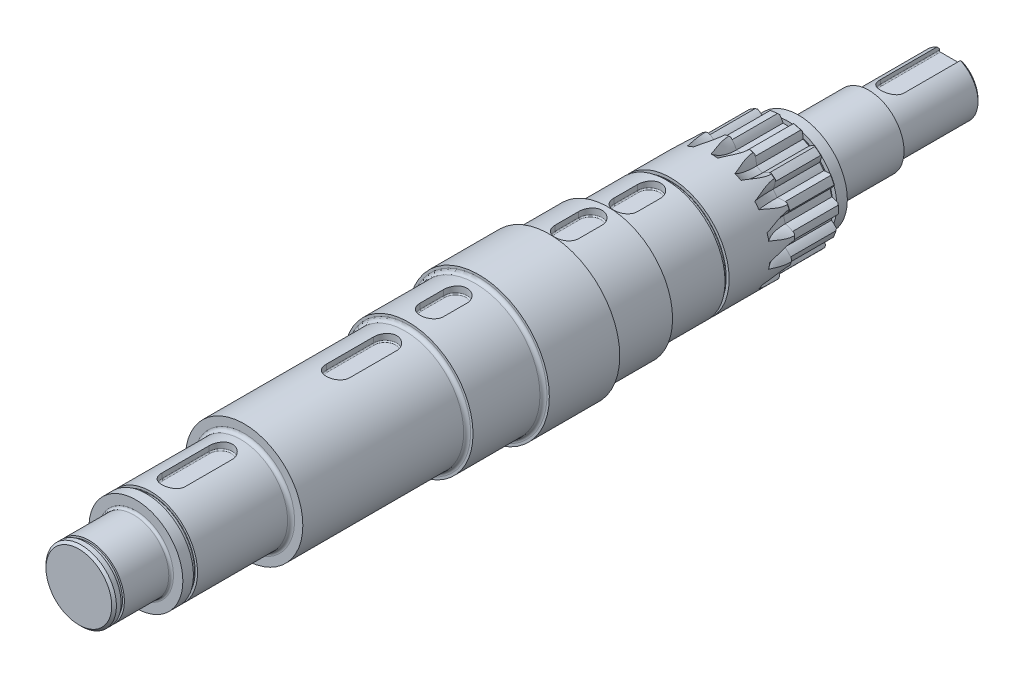
SolidWorks part; units mm, degrees
material "AISI 4340 Steel, annealed"
ref_plane "Front Plane" through (0, 0, 0) normal (0, 0, 1) x (1, 0, 0)
ref_plane "Top Plane" through (0, 0, 0) normal (0, 1, 0) x (1, 0, 0)
ref_plane "Right Plane" through (0, 0, 0) normal (1, 0, 0) x (0, 0, -1)
sketch "Sketch1" plane through (0, 0, 0) normal (1, 0, 0) x (0, 0, -1)
  line L0 (0, 0) -> (371.5, 0)
  line L2 (0, 15) -> (3, 15)
  line L3 (3, 15) -> (3, 14.175)
  line L4 (3, 14.175) -> (4.4, 14.175)
  line L5 (4.4, 14.175) -> (4.4, 15)
  line L6 (4.4, 15) -> (24.3, 15)
  line L7 (24.3, 15) -> (24.3, 20)
  line L12 (30.55, 20) -> (70.4, 20)
  line L13 (70.4, 20) -> (70.4, 25)
  line L14 (70.4, 25) -> (140.4, 25)
  line L15 (140.4, 25) -> (140.4, 27.5)
  line L16 (140.4, 27.5) -> (170.4, 27.5)
  line L20 (225.4, 25) -> (250.25, 25)
  line L21 (250.25, 25) -> (250.25, 23.6)
  line L22 (250.25, 23.6) -> (252, 23.6)
  line L23 (252, 23.6) -> (252, 25)
  line L24 (252, 25) -> (280.4, 25)
  line L25 (280.4, 25) -> (280.4, 23.85)
  line L26 (280.4, 23.85) -> (300.25, 23.85)
  line L27 (300.25, 23.85) -> (300.25, 18.85)
  line L28 (300.25, 18.85) -> (302, 18.85)
  line L29 (302, 18.85) -> (302, 20.85)
  line L30 (302, 20.85) -> (306.5, 20.85)
  line L31 (306.5, 20.85) -> (306.5, 15)
  line L32 (306.5, 15) -> (336.5, 15)
  line L34 (0, 15) -> (0, 0)
  line L35 (170.4, 27.5) -> (170.4, 30)
  line L36 (170.4, 30) -> (200.4, 30)
  line L37 (200.4, 30) -> (200.4, 27.5)
  line L38 (200.4, 27.5) -> (225.4, 27.5)
  line L39 (225.4, 27.5) -> (225.4, 25)
  line L40 (336.5, 15) -> (336.5, 12.5)
  line L41 (336.5, 12.5) -> (371.5, 12.5)
  line L42 (371.5, 12.5) -> (371.5, 0)
  line L43 (30.55, 20) -> (30.55, 18.85)
  line L44 (30.55, 18.85) -> (28.8, 18.85)
  line L45 (28.8, 18.85) -> (28.8, 20)
  line L46 (28.8, 20) -> (24.3, 20)
  point P1 (3.7, 14.175)
  dimension "D1" = 15
  dimension "D2" = 14.175
  dimension "D3" = 15
  dimension "D4" = 1.4
  dimension "D5" = 19.9
  dimension "D6" = 3
  dimension "D7" = 20
  dimension "D8" = 4.5
  dimension "D9" = 20
  dimension "D10" = 1.75
  dimension "D11" = 39.85
  dimension "D12" = 25
  dimension "D13" = 70
  dimension "D14" = 27.5
  dimension "D15" = 30
  dimension "D16" = 30
  dimension "D17" = 25
  dimension "D18" = 30
  dimension "D19" = 27.5
  dimension "D20" = 25
  dimension "D21" = 24.85
  dimension "D22" = 1.75
  dimension "D23" = 23.6
  dimension "D24" = 25
  dimension "D25" = 23.85
  dimension "D26" = 20.85
  dimension "D27" = 1.75
  dimension "D28" = 19.85
  dimension "D29" = 4.5
  dimension "D30" = 15
  dimension "D31" = 30
  dimension "D32" = 18.85
  dimension "D33" = 12.5
  dimension "D34" = 35
  dimension "D35" = 28.4
  dimension "D36" = 18.85
  dimension "D37" = 371.5
revolve "Revolve1" add sketch "Sketch1" angle 360 about L0
fillet "Fillet1" radius 1.5 5 edges at (25, 0, -225.4) (27.5, 0, -200.4) (20, 0, -70.4) (25, 0, -140.4) (27.5, 0, -170.4)
fillet "Fillet2" radius 1 3 edges at (15, 0, -306.5) (15, 0, -24.3) (12.5, 0, -336.5)
chamfer "Chamfer1" distance 1 2 edges at (12.5, 0, -371.5) (15, 0, 0)
fillet "Fillet3" radius 0.15 6 edges at (18.85, 0, -302) (18.85, 0, -300.25) (23.6, 0, -252) (23.6, 0, -250.25) (18.85, 0, -30.55) (18.85, 0, -28.8)
ref_plane "Spline_Start" through (0, 0, -300.25) normal (0, 0, -1) x (-1, 0, 0)
ref_plane "Spline_End" through (0, 0, -280.4) normal (0, 0, -1) x (-1, 0, 0)
chamfer "Chamfer3" distance 0.5 1 edges at (23.85, 0, -300.25)
sketch "Sketch2" plane through (0, 0, -300.25) normal (0, 0, -1) x (-1, 0, 0)
  line L0 (0, 0) -> (22.4675, 1.2088) construction
  line L1 (0, 0) -> (35.7993, -1.8263) construction
  arc A0 (20.7028, -2.4729) -> (20.847, 0.3533) centre (0, 0) ccw
  circle A1 centre (0, 0) radius 22.5 construction
  arc A3 (25.2715, -6.9704) -> (25.8497, 4.3624) centre (0, 0) ccw
  spline S0 degree 4 poles (19.4856, 0) (19.4973, 0.0002) (19.53, 0.0015) (19.5917, 0.0067) (19.6921, 0.019) (19.8195, 0.0404) (19.9832, 0.0744) (20.1746, 0.1227) (20.3833, 0.1844) (20.6081, 0.2607) (20.8302, 0.3448) (21.0496, 0.4362) (21.2661, 0.5339) (21.5256, 0.6599) (21.8329, 0.8219) (22.1858, 1.0265) (22.5782, 1.2766) (22.969, 1.5503) (23.3459, 1.8348) (23.7171, 2.1394) (24.0694, 2.4461) (24.4246, 2.7815) (24.7472, 3.0998) (25.0959, 3.4743) (25.3738, 3.7818) (25.7263, 4.206) (25.9302, 4.462) (26.1638, 4.7677) (26.2648, 4.9067) (26.3272, 4.9922) knots 0 0 0 0 0 0.005377 0.015084 0.028532 0.04661 0.064855 0.092111 0.119476 0.146842 0.174209 0.201575 0.228941 0.256307 0.307035 0.361767 0.4165 0.471232 0.525964 0.580697 0.635429 0.690161 0.744894 0.799626 0.854358 0.909091 0.954545 1 1 1 1 1 construction
  spline S1 degree 4 poles (20.847, 0.3533) (20.8702, 0.3626) (20.9485, 0.3943) (21.081, 0.4503) (21.2661, 0.5339) (21.5256, 0.6599) (21.8329, 0.8219) (22.1858, 1.0265) (22.5782, 1.2766) (22.969, 1.5503) (23.3459, 1.8348) (23.7171, 2.1394) (24.0694, 2.4461) (24.4246, 2.7815) (24.7472, 3.0998) (25.0959, 3.4743) (25.3738, 3.7818) (25.6498, 4.114) (25.7826, 4.2778) (25.8497, 4.3624) knots 0.162677 0.162677 0.162677 0.162677 0.162677 0.174209 0.201575 0.228941 0.256307 0.307035 0.361767 0.4165 0.471232 0.525964 0.580697 0.635429 0.690161 0.744894 0.799626 0.854358 0.909091 0.909091 0.909091 0.909091 0.909091
  spline S2 degree 4 poles (20.7028, -2.4729) (20.725, -2.4846) (20.7996, -2.5241) (20.9257, -2.5933) (21.1014, -2.6953) (21.3467, -2.8471) (21.6359, -3.0395) (21.9661, -3.279) (22.3311, -3.5677) (22.692, -3.8797) (23.038, -4.2011) (23.3763, -4.5419) (23.6955, -4.8829) (24.0148, -5.2527) (24.3032, -5.6021) (24.6121, -6.0102) (24.8572, -6.3444) (25.098, -6.703) (25.2134, -6.8794) (25.2715, -6.9704) knots 0.162677 0.162677 0.162677 0.162677 0.162677 0.174209 0.201575 0.228941 0.256307 0.307035 0.361767 0.4165 0.471232 0.525964 0.580697 0.635429 0.690161 0.744894 0.799626 0.854358 0.909091 0.909091 0.909091 0.909091 0.909091
  dimension "D1" = 45
  dimension "D2" = 41.7
  dimension "D4" = 6
extrude "Cut-Extrude1" cut sketch "Sketch2" against normal up to surface (19.85 mm away) up to plane "Spline_End"
chamfer "Chamfer2" distance 0.5 1 edges at (25, 0, -280.4)
sketch "Sketch4" plane through (0, 0, -280.4) normal (0, 0, -1) x (-1, 0, 0)
  line L0 (0, 0) -> (22.2279, -3.4889) construction
  line L1 (0, 0) -> (22.4675, 1.2088) construction
  line L2 (0, 0) -> (47.6551, -2.4312) construction
  line L3 (37.6409, 2.4855) -> (37.1925, -6.3031)
  line L5 (24.3333, -5.6471) -> (37.1925, -6.3031)
  line L7 (24.7817, 3.1415) -> (37.6409, 2.4855)
  circle A0 centre (0, 0) radius 22.5 construction
  arc A2 (20.7028, -2.4729) -> (20.847, 0.3533) centre (0, 0) ccw
  arc A3 (25.2715, -6.9704) -> (25.8497, 4.3624) centre (0, 0) ccw
  arc A4 (20.7028, -2.4729) -> (20.847, 0.3533) centre (0, 0) ccw
  spline S2 degree 4 poles (1889.3076, 2355.0093) (-24.1348, -57.4522) (30.594, 10.6482) (26.4975, 5.0256) (25.0959, 3.4743) (24.7472, 3.0998) (24.4246, 2.7815) (24.0694, 2.4461) (23.7171, 2.1394) (23.3459, 1.8348) (22.969, 1.5503) (22.5782, 1.2766) (22.1858, 1.0265) (21.8329, 0.8219) (21.5256, 0.6599) (21.2661, 0.5339) (15.0924, -2.2517) (5.8252, 1.7027) (6.0901, 65.8486) (-2316.7827, -1878.7907) knots -0.722695 -0.722695 -0.722695 -0.722695 -0.722695 0.217409 0.272142 0.326874 0.381606 0.436339 0.491071 0.545804 0.600536 0.655268 0.71 0.764733 0.81546 0.842827 0.870193 0.897559 3.937545 3.937545 3.937545 3.937545 3.937545 only from (25.8497, 4.3624) to (20.847, 0.3533)
  spline S3 degree 4 poles (-2113.5242, 2104.7727) (-0.6426, -66.1258) (5.6218, -2.2866) (15.2432, 0.7041) (21.1014, -2.6953) (21.3467, -2.8471) (21.6359, -3.0395) (21.9661, -3.279) (22.3311, -3.5677) (22.692, -3.8797) (23.038, -4.2011) (23.3763, -4.5419) (23.6955, -4.8829) (24.0148, -5.2527) (24.3032, -5.6021) (24.6121, -6.0102) (25.8485, -7.696) (29.3517, -13.7065) (-18.1655, 59.6142) (1639.9724, -2535.2599) knots -2.865766 -2.865766 -2.865766 -2.865766 -2.865766 0.174209 0.201575 0.228941 0.256307 0.307035 0.361767 0.4165 0.471232 0.525964 0.580697 0.635429 0.690161 0.744894 0.799626 0.854358 1.794481 1.794481 1.794481 1.794481 1.794481 only from (20.7028, -2.4729) to (25.2715, -6.9704)
  spline S4 degree 4 poles (24.7817, 3.1415) (24.7324, 3.0903) (24.5996, 2.9544) (24.388, 2.747) (24.0694, 2.4461) (23.7171, 2.1394) (23.3459, 1.8348) (22.969, 1.5503) (22.5782, 1.2766) (22.1858, 1.0265) (21.8329, 0.8219) (21.5256, 0.6599) (21.2661, 0.5339) (21.081, 0.4503) (20.9485, 0.3943) (20.8702, 0.3626) (20.847, 0.3533) knots 0.349431 0.349431 0.349431 0.349431 0.349431 0.381606 0.436339 0.491071 0.545804 0.600536 0.655268 0.71 0.764733 0.81546 0.842827 0.870193 0.897559 0.909091 0.909091 0.909091 0.909091 0.909091
  spline S5 degree 4 poles (20.7028, -2.4729) (20.725, -2.4846) (20.7996, -2.5241) (20.9257, -2.5933) (21.1014, -2.6953) (21.3467, -2.8471) (21.6359, -3.0395) (21.9661, -3.279) (22.3311, -3.5677) (22.692, -3.8797) (23.038, -4.2011) (23.3763, -4.5419) (23.6955, -4.8829) (23.9819, -5.2146) (24.1712, -5.4425) (24.2895, -5.5912) (24.3333, -5.6471) knots 0.162677 0.162677 0.162677 0.162677 0.162677 0.174209 0.201575 0.228941 0.256307 0.307035 0.361767 0.4165 0.471232 0.525964 0.580697 0.635429 0.690161 0.722337 0.722337 0.722337 0.722337 0.722337
  dimension "D2" = 45
  dimension "D3" = 6
  dimension "D1" = 0
revolve "Cut-Revolve2" cut sketch "Sketch4" angle 360 about L3
pattern_circular "CirPattern1" count 15 over 360 about axis through (0, 0, 0) along (0, 0, 1) of "Cut-Extrude1", "Cut-Revolve2"
ref_plane "Reverse_Gear_Key" through (0, 20, 0) normal (0, 1, 0) x (1, 0, 0)
sketch "Sketch5" plane through (0, 20, 0) normal (0, 1, 0) x (1, 0, 0)
  line L0 (-25, 70.4) -> (25, 70.4) construction
  line L1 (-25, 70.4) -> (25, 70.4) construction
  line L2 (0, 70.4) -> (0, 60.4) construction
  line L3 (0, 60.4) -> (0, 40.4) construction
  line L4 (-5, 60.4) -> (-5, 40.4)
  line L5 (5, 60.4) -> (5, 40.4)
  arc A0 (-5, 60.4) -> (5, 60.4) centre (0, 60.4) cw
  arc A1 (-5, 40.4) -> (5, 40.4) centre (0, 40.4) ccw
  dimension "D1" = 10
  dimension "D2" = 20
  dimension "D3" = 5
  dimension "D4" = 5
ref_plane "Gear_1_Key" through (0, 25, 0) normal (0, 1, 0) x (1, 0, 0)
sketch "Sketch6" plane through (0, 25, 0) normal (0, 1, 0) x (1, 0, 0)
  line L0 (-27.5, 140.4) -> (27.5, 140.4) construction
  line L1 (-27.5, 140.4) -> (27.5, 140.4) construction
  line L2 (0, 140.4) -> (0, 130.4) construction
  line L3 (0, 130.4) -> (0, 110.4) construction
  line L4 (-5, 130.4) -> (-5, 110.4)
  line L5 (5, 130.4) -> (5, 110.4)
  arc A0 (-5, 130.4) -> (5, 130.4) centre (0, 130.4) cw
  arc A1 (-5, 110.4) -> (5, 110.4) centre (0, 110.4) ccw
  dimension "D1" = 10
  dimension "D2" = 20
  dimension "D3" = 5
  dimension "D4" = 5
ref_plane "Gear_2_Key" through (0, 27.5, 0) normal (0, 1, 0) x (1, 0, 0)
sketch "Sketch7" plane through (0, 27.5, 0) normal (0, 1, 0) x (1, 0, 0)
  line L0 (-30, 170.4) -> (30, 170.4) construction
  line L1 (-30, 170.4) -> (30, 170.4) construction
  line L2 (0, 170.4) -> (0, 160.4) construction
  line L3 (0, 160.4) -> (0, 150.4) construction
  line L4 (-5, 160.4) -> (-5, 150.4)
  line L5 (5, 160.4) -> (5, 150.4)
  arc A0 (-5, 160.4) -> (5, 160.4) centre (0, 160.4) cw
  arc A1 (-5, 150.4) -> (5, 150.4) centre (0, 150.4) ccw
  dimension "D1" = 10
  dimension "D2" = 10
  dimension "D3" = 5
  dimension "D4" = 5
ref_plane "Gear_3_Key" through (0, 27.5, 0) normal (0, 1, 0) x (1, 0, 0)
sketch "Sketch8" plane through (0, 27.5, 0) normal (0, 1, 0) x (1, 0, 0)
  line L0 (30, 200.4) -> (-30, 200.4) construction
  line L1 (30, 200.4) -> (-30, 200.4) construction
  line L2 (0, 200.4) -> (0, 207.9) construction
  line L3 (0, 207.9) -> (0, 217.9) construction
  line L4 (5, 207.9) -> (5, 217.9)
  line L5 (-5, 207.9) -> (-5, 217.9)
  arc A0 (5, 207.9) -> (-5, 207.9) centre (0, 207.9) cw
  arc A1 (5, 217.9) -> (-5, 217.9) centre (0, 217.9) ccw
  dimension "D1" = 7.5
  dimension "D2" = 10
  dimension "D3" = 5
  dimension "D4" = 5
ref_plane "Gear_4_Key" through (0, 25, 0) normal (0, 1, 0) x (1, 0, 0)
sketch "Sketch9" plane through (0, 25, 0) normal (0, 1, 0) x (1, 0, 0)
  line L0 (27.5, 225.4) -> (-27.5, 225.4) construction
  line L1 (27.5, 225.4) -> (-27.5, 225.4) construction
  line L2 (0, 225.4) -> (0, 232.9) construction
  line L3 (0, 232.9) -> (0, 242.9) construction
  line L4 (5, 232.9) -> (5, 242.9)
  line L5 (-5, 232.9) -> (-5, 242.9)
  arc A0 (5, 232.9) -> (-5, 232.9) centre (0, 232.9) cw
  arc A1 (5, 242.9) -> (-5, 242.9) centre (0, 242.9) ccw
  dimension "D1" = 7.5
  dimension "D2" = 10
  dimension "D3" = 5
  dimension "D4" = 5
extrude "Cut-Extrude3" cut sketch "Sketch5" against normal blind 3.2
extrude "Cut-Extrude4" cut sketch "Sketch6" against normal blind 3.2
extrude "Cut-Extrude5" cut sketch "Sketch7" against normal blind 3.2
extrude "Cut-Extrude6" cut sketch "Sketch8" against normal blind 3.2
extrude "Cut-Extrude7" cut sketch "Sketch9" against normal blind 3.2
ref_plane "Flange_Key" through (0, 12.5, 0) normal (0, 1, 0) x (1, 0, 0)
sketch "Sketch10" plane through (0, 12.5, 0) normal (0, 1, 0) x (1, 0, 0)
  line L0 (11.5, 371.5) -> (-11.5, 371.5) construction
  line L1 (11.5, 371.5) -> (-11.5, 371.5) construction
  line L2 (0, 371.5) -> (0, 346.5) construction
  line L3 (-5, 371.5) -> (-5, 346.5)
  line L4 (5, 371.5) -> (5, 346.5)
  arc A0 (-5, 371.5) -> (5, 371.5) centre (0, 371.5) cw
  arc A1 (-5, 346.5) -> (5, 346.5) centre (0, 346.5) ccw
  dimension "D1" = 25
  dimension "D2" = 5
  dimension "D3" = 5
extrude "Cut-Extrude8" cut sketch "Sketch10" against normal blind 3.2
fillet "Fillet5" radius 0.5 23 edges at (5, 9.3, -359) (0, 9.3, -341.5) (-5, 9.3, -359) (0, 16.8, -65.4) (5, 16.8, -50.4) (0, 16.8, -35.4) (0, 21.8, -135.4) (5, 21.8, -120.4) (0, 21.8, -105.4) (0, 24.3, -165.4) (5, 24.3, -155.4) (0, 24.3, -145.4) (0, 24.3, -222.9) (5, 24.3, -212.9) (0, 24.3, -202.9) (0, 21.8, -247.9) (5, 21.8, -237.9) (0, 21.8, -227.9) (-5, 16.8, -50.4) (-5, 21.8, -120.4) (-5, 24.3, -155.4) (-5, 24.3, -212.9) (-5, 21.8, -237.9)
